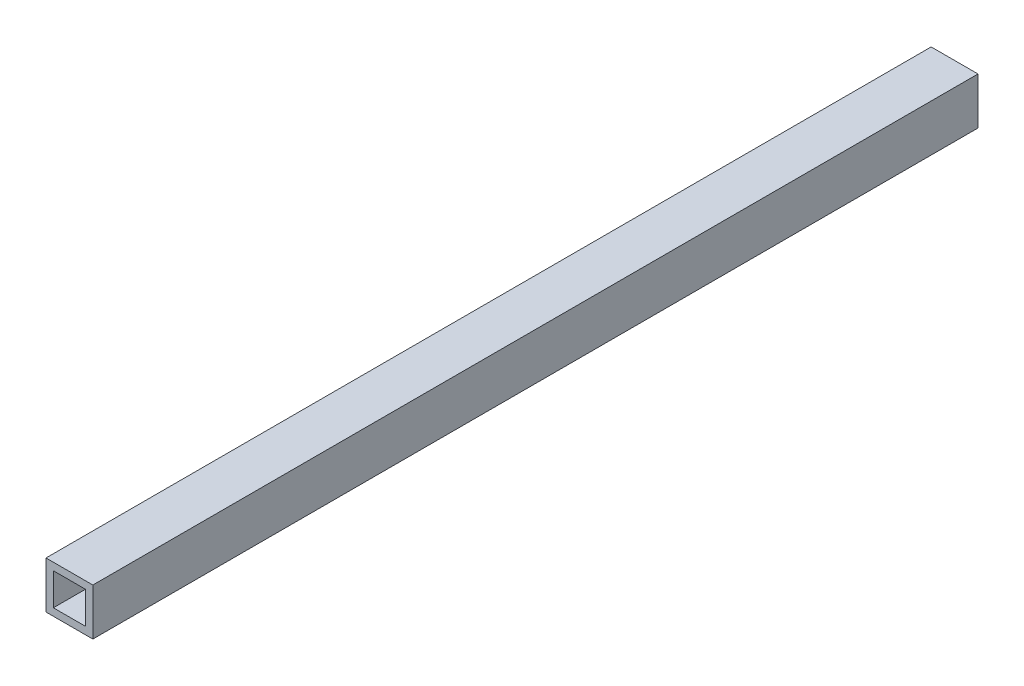
SolidWorks part; units mm, degrees
ref_plane "Front Plane" through (0, 0, 0) normal (0, 0, 1) x (1, 0, 0)
ref_plane "Top Plane" through (0, 0, 0) normal (0, 1, 0) x (1, 0, 0)
ref_plane "Right Plane" through (0, 0, 0) normal (1, 0, 0) x (0, 0, -1)
sketch "Sketch1" plane through (0, 0, 0) normal (0, 0, 1) x (1, 0, 0)
  line L0 (4.35, 4.35) -> (-4.35, 4.35)
  line L1 (6.35, 6.35) -> (-6.35, 6.35)
  line L2 (6.35, 6.35) -> (6.35, -6.35)
  line L3 (6.35, -6.35) -> (-6.35, -6.35)
  line L4 (-6.35, 6.35) -> (-6.35, -6.35)
  line L5 (6.35, 6.35) -> (-6.35, -6.35) construction
  line L6 (6.35, -6.35) -> (-6.35, 6.35) construction
  line L7 (-4.35, 4.35) -> (-4.35, -4.35)
  line L8 (4.35, -4.35) -> (-4.35, -4.35)
  line L9 (4.35, 4.35) -> (4.35, -4.35)
  point P0 (0, 0)
  dimension "D1" = 12.7
  dimension "D2" = 2
extrude "Boss-Extrude1" add sketch "Sketch1" along normal blind 240
